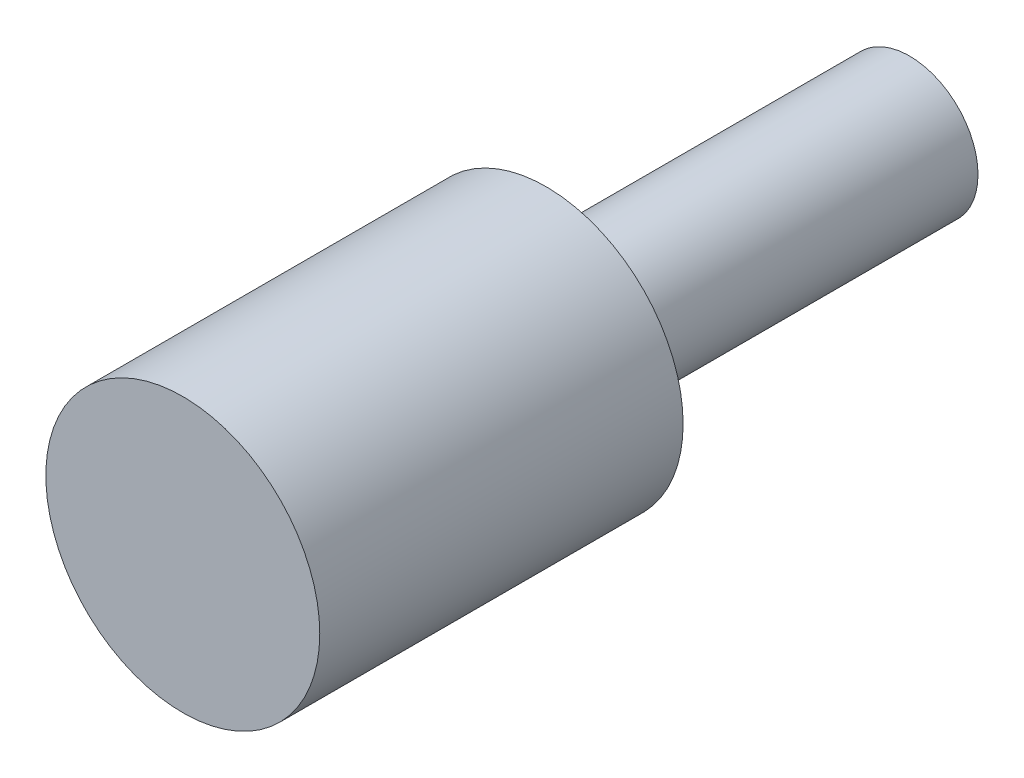
SolidWorks part; units mm, degrees
material "AISI 1020"
ref_plane "Front Plane" through (0, 0, 0) normal (0, 0, 1) x (1, 0, 0)
ref_plane "Top Plane" through (0, 0, 0) normal (0, 1, 0) x (1, 0, 0)
ref_plane "Right Plane" through (0, 0, 0) normal (1, 0, 0) x (0, 0, -1)
sketch "Sketch1" plane through (0, 0, 0) normal (0, 0, 1) x (1, 0, 0)
  circle A0 centre (0, 0) radius 6.223
  dimension "D1" = 12.446
extrude "Boss-Extrude1" add sketch "Sketch1" along normal blind 33.02
sketch "Sketch2" plane through (0, 0, 33.02) normal (0, 0, 1) x (1, 0, 0)
  circle A0 centre (0, 0) radius 12.446
  dimension "D1" = 24.892
extrude "Boss-Extrude2" add sketch "Sketch2" along normal blind 33.02
